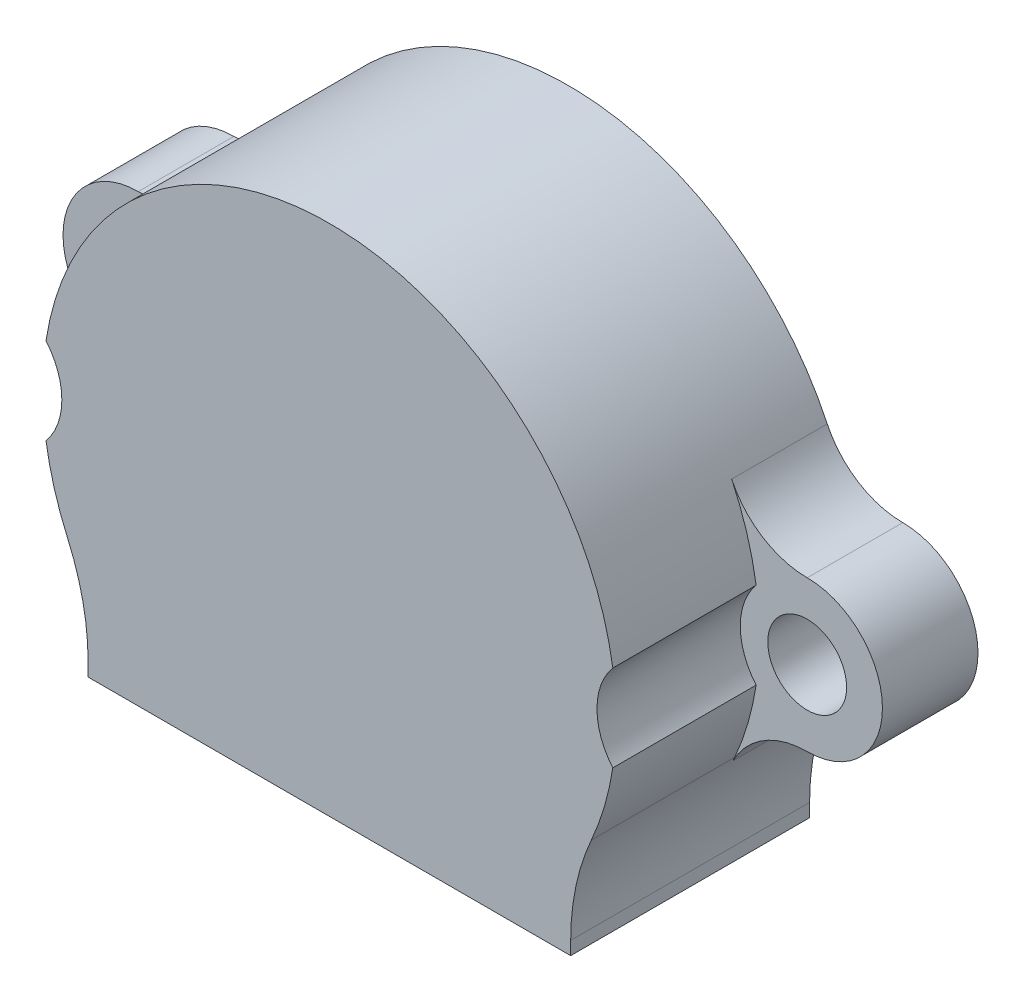
SolidWorks part; units mm, degrees
ref_plane "Front Plane" through (0, 0, 0) normal (0, 0, 1) x (1, 0, 0)
ref_plane "Top Plane" through (0, 0, 0) normal (0, 1, 0) x (1, 0, 0)
ref_plane "Right Plane" through (0, 0, 0) normal (1, 0, 0) x (0, 0, -1)
sketch "Sketch1" plane through (0, 0, 0) normal (0, 0, 1) x (1, 0, 0)
  line L0 (0, 0) -> (0, 12) construction
  line L1 (-7.6, -4.1307) -> (-7.6, -9.5)
  line L3 (7.6, -9.5) -> (7.6, -4.1307)
  line L4 (-7.6, -9.5) -> (-10.1, -9.5)
  line L5 (-10.1, -9.5) -> (-10.1, -6.48)
  line L6 (10.1, -6.48) -> (10.1, -9.5)
  line L7 (10.1, -9.5) -> (7.6, -9.5)
  arc A0 (7.6, -4.1307) -> (-7.6, -4.1307) centre (0, 0) ccw
  arc A1 (10.1, -6.48) -> (-10.1, -6.48) centre (0, 0) ccw
  dimension "D1" = 17.3
  dimension "D2" = 24
  dimension "D3" = 15.2
  dimension "D4" = 2.5
  dimension "D5" = 9.5
extrude "Boss-Extrude1" add sketch "Sketch1" along normal blind 10
sketch "Sketch2" plane through (0, 0, 10) normal (0, 0, 1) x (1, 0, 0)
  line L0 (7.6, -4.1307) -> (7.6, -9.5) construction
  line L1 (-7.6, -9.5) -> (-7.6, -4.1307) construction
  line L2 (7.6, -4.1307) -> (7.6, -9.5)
  line L3 (-7.6, -9.5) -> (-7.6, -4.1307)
  line L4 (-7.6, -9.5) -> (7.6, -9.5)
  arc A0 (7.6, -4.1307) -> (-7.6, -4.1307) centre (0, 0) ccw construction
  arc A1 (7.6, -4.1307) -> (-7.6, -4.1307) centre (0, 0) ccw
extrude "Boss-Extrude2" add sketch "Sketch2" against normal blind 0.8
fillet "Fillet1" radius 10 2 edges at (-10.1, -6.48, 5) (10.1, -6.48, 5)
sketch "Sketch3" plane through (0, 0, 0) normal (0, 0, -1) x (-1, 0, 0)
  line L0 (0, 0) -> (14, 0) construction
  line L1 (0, 0) -> (0, 12) construction
  circle A0 centre (14, 0) radius 1.65
  arc A1 (10.9636, -4.8784) -> (-10.9636, -4.8784) centre (0, 0) ccw construction
  arc A2 (14, 3.15) -> (14, -3.15) centre (14, 0) cw
  arc A3 (14, -3.15) -> (10.8398, -5.1477) centre (14, -6.6484) ccw
  arc A5 (14, 3.15) -> (10.8398, 5.1477) centre (14, 6.6484) cw
  arc A14 (10.8398, 5.1477) -> (10.8398, -5.1477) centre (0, 0) cw
  arc A15 (-10.8398, 5.1477) -> (-10.8398, -5.1477) centre (0, 0) ccw
  arc A16 (-14, 3.15) -> (-10.8398, 5.1477) centre (-14, 6.6484) ccw
  arc A17 (-14, -3.15) -> (-10.8398, -5.1477) centre (-14, -6.6484) cw
  arc A18 (-14, 3.15) -> (-14, -3.15) centre (-14, 0) ccw
  circle A19 centre (-14, 0) radius 1.65
  dimension "D1" = 3.3
  dimension "D2" = 1.5
  dimension "D3" = 14
extrude "Boss-Extrude4" add sketch "Sketch3" against normal blind 4
sketch "Sketch4" plane through (0, 0, 4) normal (0, 0, 1) x (1, 0, 0)
  circle A0 centre (-14, 0) radius 2.8
  circle A1 centre (14, 0) radius 2.8
  dimension "D1" = 5.6
extrude "Cut-Extrude1" cut sketch "Sketch4" along normal through all
